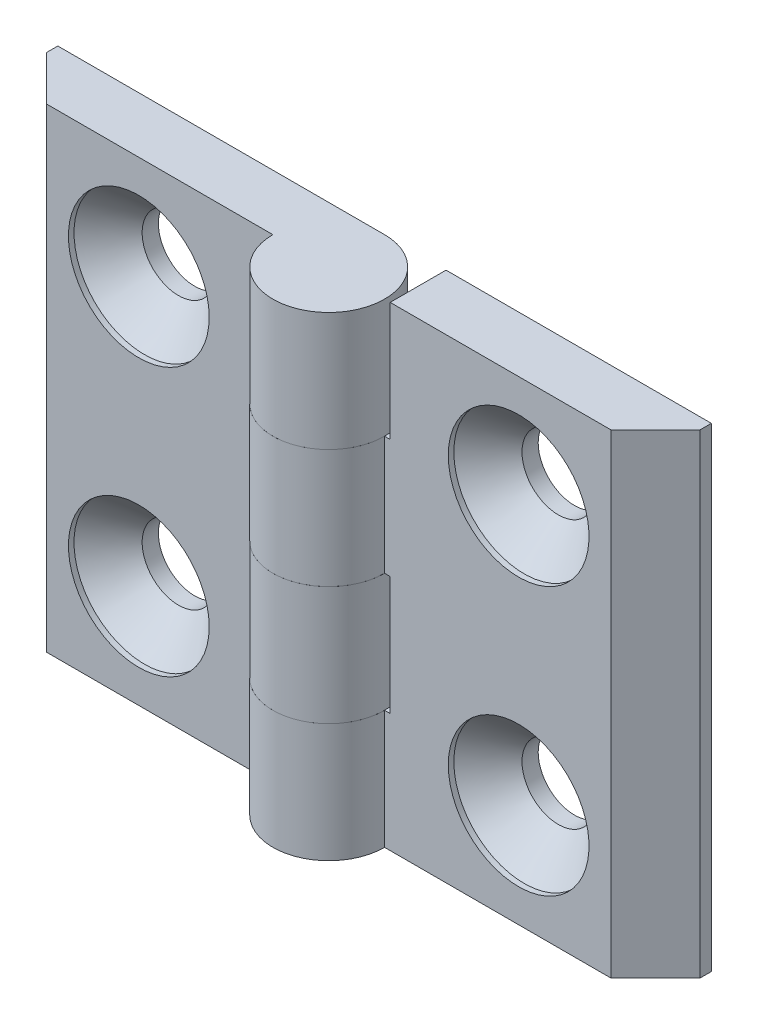
SolidWorks part; units mm, degrees
material "Алюминиевый сплав"
ref_plane "Спереди" through (0, 0, 0) normal (0, 0, 1) x (1, 0, 0)
ref_plane "Сверху" through (0, 0, 0) normal (0, 1, 0) x (1, 0, 0)
ref_plane "Справа" through (0, 0, 0) normal (1, 0, 0) x (0, 0, -1)
sketch "Эскиз1" plane through (0, 0, 0) normal (0, 1, 0) x (1, 0, 0)
  line L0 (0, 5) -> (-29.25, 5)
  line L1 (-29.25, 5) -> (-29.25, 4)
  line L2 (-29.25, 4) -> (-25.25, 0)
  line L3 (-25.25, 0) -> (-5, 0)
  line L4 (0, 0) -> (0, 10.5526) construction
  arc A0 (-5, 0) -> (0, 5) centre (0, 0) ccw
  dimension "D1" = 58.5
  dimension "D2" = 5
  dimension "D3" = 1
  dimension "D4" = 45
extrude "Бобышка-Вытянуть1" add sketch "Эскиз1" along normal mid plane 42.5
sketch "Эскиз3" plane through (0, 0, 0) normal (0, 0, 1) x (1, 0, 0)
  line L0 (5, -21.25) -> (5, 21.25) construction
  line L1 (-5.5, 10.625) -> (5, 10.625)
  line L2 (-5.5, 10.625) -> (-5.5, 0)
  line L3 (-5.5, 0) -> (5, 0)
  line L4 (5, 10.625) -> (5, 0)
  line L5 (5, 0) -> (5, -10.625) construction
  line L6 (5, -21.25) -> (-5.5, -21.25)
  line L7 (5, -21.25) -> (5, -10.625)
  line L8 (5, -10.625) -> (-5.5, -10.625)
  line L9 (-5.5, -21.25) -> (-5.5, -10.625)
  line L10 (5, 10.625) -> (5, 21.25) construction
  line L11 (-5, 21.25) -> (-5, -21.25) construction
  dimension "D1" = 0.5
extrude "Вырез-Вытянуть1" cut sketch "Эскиз3" against normal through all and the other way through all
hole_wizard "Зенковка для винта с полупотайной головкой M61" positions "Эскиз4" profile "Эскиз6" countersink size "M6" standard "ISO" end condition through all
sketch "Эскиз4" plane through (0, 0, 0) normal (0, 0, 1) x (1, 0, 0)
  line L0 (-17, 12) -> (-17, -12)
  line L2 (0, 0) -> (0, 18.9001) construction
  line L3 (5, 0) -> (-5, 0) construction
  point P0 (-17, 12)
  point P2 (-17, -12)
  point P9 (-17, 0)
  dimension "D1" = 24
  dimension "D2" = 34
sketch "Эскиз6" plane through (-17, 12, 0) normal (1, 0, 0) x (0, -1, 0)
  line L0 (0, 0) -> (0, 5)
  line L1 (0, 5) -> (3.25, 5)
  line L2 (3.25, 5) -> (3.25, 3.55)
  line L3 (3.25, 3.55) -> (6.3, 0.5)
  line L4 (6.3, 0.5) -> (6.3, 0)
  line L6 (6.3, 0) -> (0, 0)
  line L7 (-3.25, 3.55) -> (-6.3, 0.5) construction
  line L11 (0, -6.35) -> (0, 107.95) construction
  dimension "Диаметр сквозного отверстия" = 6.5
  dimension "Глубина сквозного отверстия" = 5
  dimension "Диаметр зенковки" = 12.6
  dimension "Угол зенковки" = 90
  dimension "Утопленность" = 0.5
sketch "Угол раскрытия" plane through (0, 0, 0) normal (0, 1, 0) x (1, 0, 0)
  line L0 (0, 0) -> (0, -10)
  line L7 (0, 5) -> (-29.25, 5) construction
  point P3 (-11.2006, -8.7746)
  point P8 (-7.4924, -9.3736)
  point P9 (0, 0)
  point P10 (-11.8016, -2.1731)
  dimension "D1" = 10
  dimension "D2" = 90
pattern_circular "Круговой массив1" count 2 over 360 about axis through (0, 0, 0) along (0, 0, 1) of bodies 106
